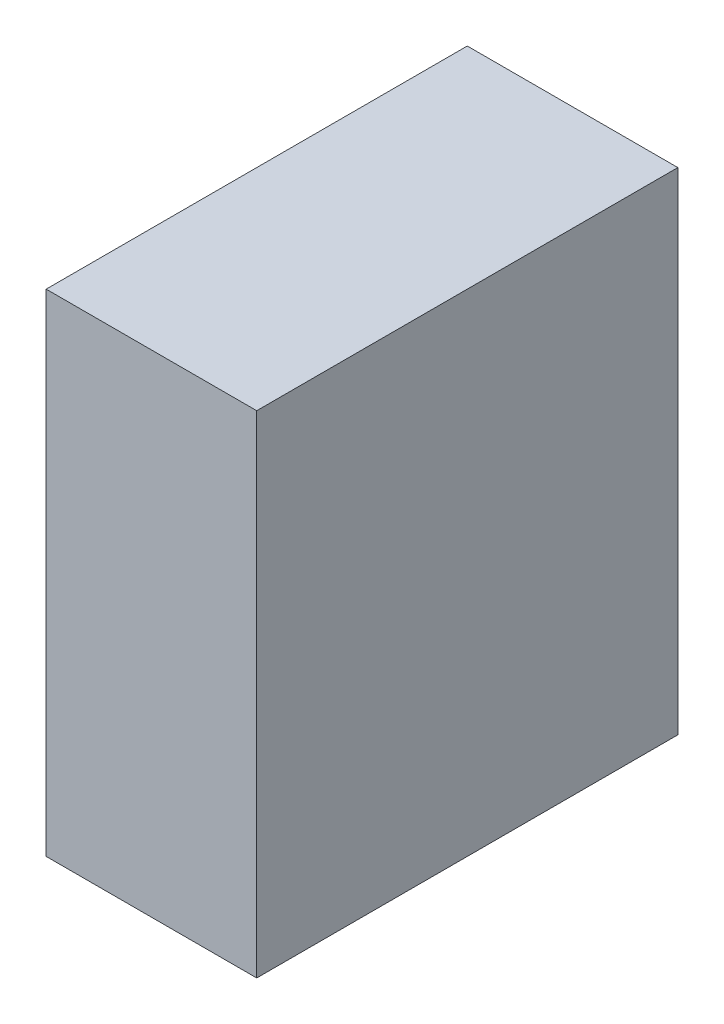
SolidWorks part; units mm, degrees
ref_plane "Plan de face" through (0, 0, 0) normal (0, 0, 1) x (1, 0, 0)
ref_plane "Plan de dessus" through (0, 0, 0) normal (0, 1, 0) x (1, 0, 0)
ref_plane "Plan de droite" through (0, 0, 0) normal (1, 0, 0) x (0, 0, -1)
sketch "Esquisse1" plane through (0, 0, 0) normal (0, 0, 1) x (1, 0, 0)
  line L1 (0, 0) -> (30, 0)
  line L2 (0, 0) -> (0, 70)
  line L3 (0, 70) -> (30, 70)
  line L4 (30, 0) -> (30, 70)
  dimension "D1" = 30
  dimension "D2" = 70
extrude "Boss.-Extru.1" add sketch "Esquisse1" along normal blind 60
